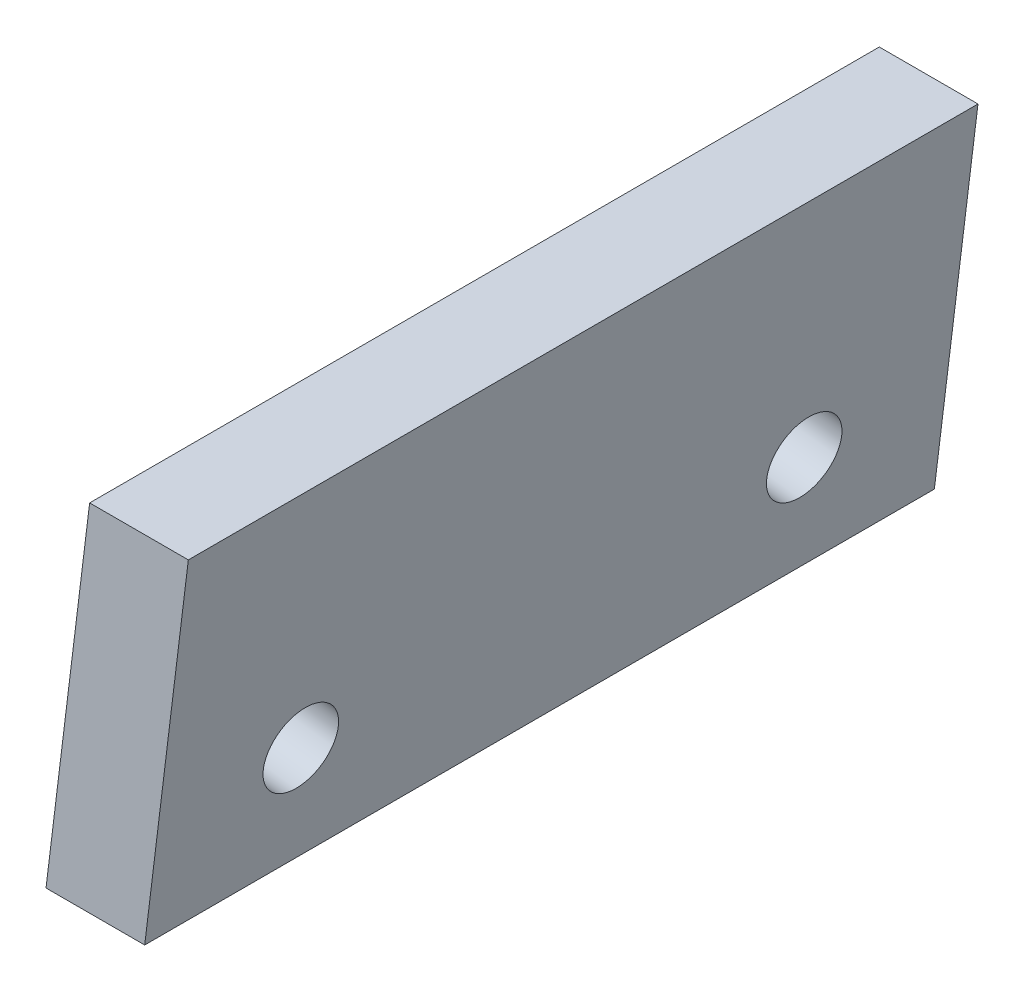
SolidWorks part; units mm, degrees
ref_plane "Front Plane" through (0, 0, 0) normal (0, 0, 1) x (1, 0, 0)
ref_plane "Top Plane" through (0, 0, 0) normal (0, 1, 0) x (1, 0, 0)
ref_plane "Right Plane" through (0, 0, 0) normal (1, 0, 0) x (0, 0, -1)
sketch "Sketch2" plane through (0, 0, 0) normal (0, 0, 1) x (1, 0, 0)
  line L0 (0, 0) -> (2.5, 0)
  line L1 (0, 0) -> (1.1051, 9)
  line L2 (2.5, 0) -> (3.6051, 9)
  line L3 (3.6051, 9) -> (1.1051, 9)
  line L4 (2.5, 0) -> (7.5011, 0) construction
  dimension "D1" = 9
  dimension "D2" = 2.5
  dimension "D3" = 83
extrude "Boss-Extrude2" add sketch "Sketch2" along normal blind 20
sketch "Sketch4" plane through (0, 0, 0) normal (-0.9925, 0.1219, 0) x (0, 0, 1)
  line L0 (0, 9.0676) -> (0, 0) construction
  line L1 (20, 9.0676) -> (20, 0) construction
  line L2 (20, 0) -> (0, 0) construction
  circle A0 centre (3.625, 3) radius 0.95
  circle A1 centre (16.375, 3) radius 0.95
  dimension "D1" = 3.625
  dimension "D2" = 3.625
  dimension "D3" = 3
  dimension "D4" = 3
  dimension "D5" = 1.9
  dimension "D6" = 1.9
extrude "Cut-Extrude1" cut sketch "Sketch4" against normal through all
